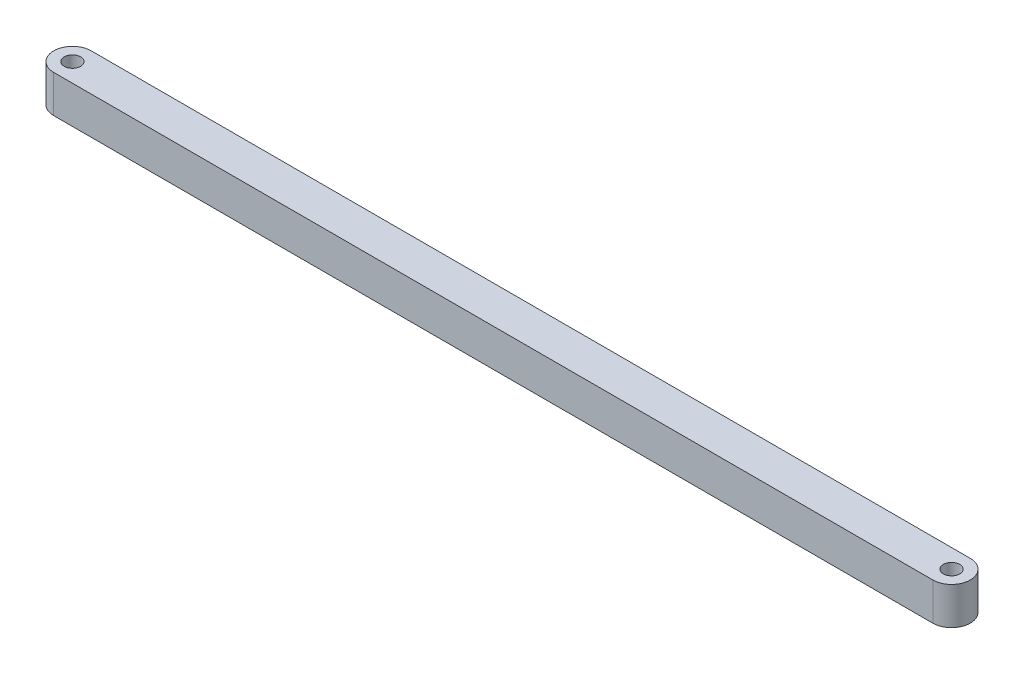
SolidWorks part; units mm, degrees
ref_plane "Front Plane" through (0, 0, 0) normal (0, 0, 1) x (1, 0, 0)
ref_plane "Top Plane" through (0, 0, 0) normal (0, 1, 0) x (1, 0, 0)
ref_plane "Right Plane" through (0, 0, 0) normal (1, 0, 0) x (0, 0, -1)
sketch "Sketch1" plane through (0, 0, 0) normal (0, 1, 0) x (1, 0, 0)
  line L1 (-58.7, 2.5) -> (58.7, 2.5)
  line L2 (58.6848, -2.5) -> (-58.7, -2.5)
  circle A0 centre (-58.7, 0) radius 1.1
  circle A1 centre (58.6848, 0) radius 1.1
  arc A2 (-58.7, 2.5) -> (-58.7, -2.5) centre (-58.7, 0) ccw
  arc A3 (58.6848, -2.5) -> (58.7, 2.5) centre (58.6848, 0) ccw
  point P4 (0, 0)
  dimension "D1" = 2.2
  dimension "D2" = 2.2
  dimension "D3" = 5
  dimension "D4" = 5
  dimension "D5" = 117.3848
extrude "Boss-Extrude1" add sketch "Sketch1" along normal blind 5
